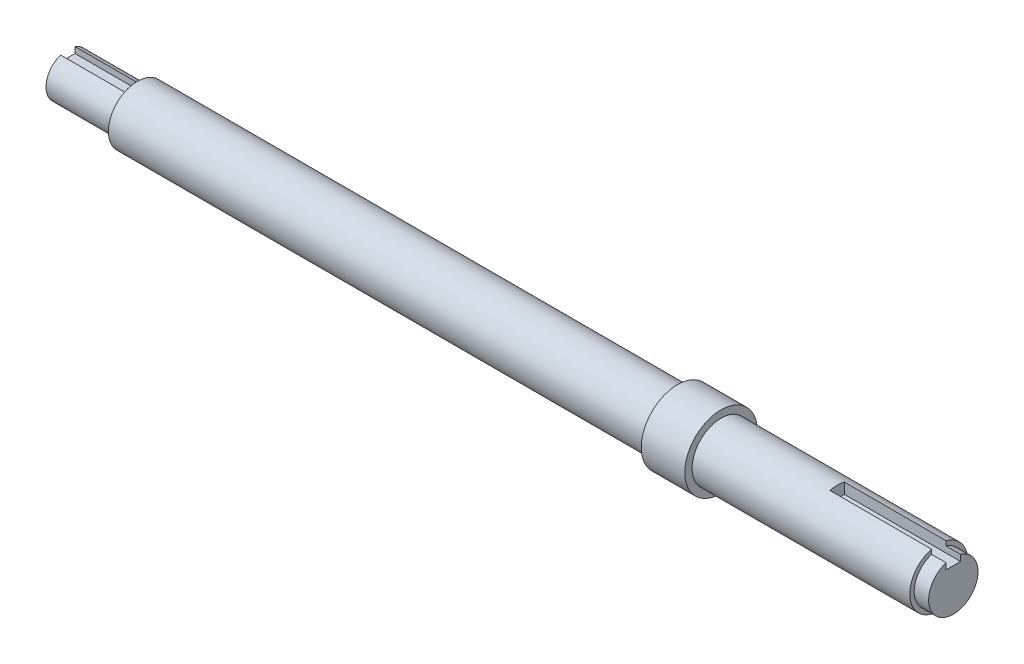
SolidWorks part; units mm, degrees
material "6061-T6 (SS)"
ref_plane "Front Plane" through (0, 0, 0) normal (0, 0, 1) x (1, 0, 0)
ref_plane "Top Plane" through (0, 0, 0) normal (0, 1, 0) x (1, 0, 0)
ref_plane "Right Plane" through (0, 0, 0) normal (1, 0, 0) x (0, 0, -1)
sketch "Sketch1" plane through (0, 0, 0) normal (1, 0, 0) x (0, 0, -1)
  circle A0 centre (0, 0) radius 10
  dimension "D1" = 20
extrude "Boss-Extrude1" add sketch "Sketch1" along normal blind 300
sketch "Sketch2" plane through (300, 0, 0) normal (1, 0, 0) x (0, 0, -1)
  circle A0 centre (0, 0) radius 8.5
  dimension "D1" = 17
extrude "Boss-Extrude2" add sketch "Sketch2" along normal blind 5
sketch "Sketch6" plane through (0, 0, 0) normal (-1, 0, 0) x (0, 0, 1)
  line L0 (-2.5, 7.0711) -> (-2.5, 5)
  line L1 (-2.5, 5) -> (2.5, 5)
  line L2 (2.5, 5) -> (2.5, 7.0711)
  circle A0 centre (0, 0) radius 10
  arc A1 (-2.5, 7.0711) -> (2.5, 7.0711) centre (0, 0) ccw
  point P6 (0, 5)
  dimension "D1" = 15
  dimension "D2" = 5
  dimension "D3" = 5
extrude "Cut-Extrude2" cut sketch "Sketch6" against normal blind 24
sketch "Sketch7" plane through (305, 0, 0) normal (1, 0, 0) x (0, 0, -1)
  line L1 (-2.5, 6) -> (2.5, 6)
  line L2 (-2.5, 6) -> (-2.5, 11)
  line L3 (-2.5, 11) -> (2.5, 11)
  line L4 (2.5, 6) -> (2.5, 11)
  line L5 (-2.5, 6) -> (2.5, 11) construction
  line L6 (-2.5, 11) -> (2.5, 6) construction
  circle A0 centre (0, 0) radius 8.5 construction
  point P0 (0, 8.5)
  dimension "D1" = 5
  dimension "D2" = 5
extrude "Cut-Extrude3" cut sketch "Sketch7" against normal blind 40
sketch "Sketch8" plane through (305, 0, 0) normal (1, 0, 0) x (0, 0, -1)
  circle A0 centre (0, 0) radius 9.9522
  circle A1 centre (0, 0) radius 8
  dimension "D1" = 16
sketch "Sketch9" plane through (24, 0, 0) normal (-1, 0, 0) x (0, 0, 1)
  circle A0 centre (0, 0) radius 9.5
  dimension "D1" = 19
extrude "Boss-Extrude3" [suppressed] add sketch "Sketch9" against normal up to surface (241 mm away)
ref_plane "Plane1" through (225, 0, 0) normal (1, 0, 0) x (0, 0, -1)
sketch "Sketch10" plane through (225, 0, 0) normal (1, 0, 0) x (0, 0, -1)
  circle A0 centre (0, 0) radius 12.5
  dimension "D1" = 25
extrude "Boss-Extrude4" add sketch "Sketch10" against normal blind 15
